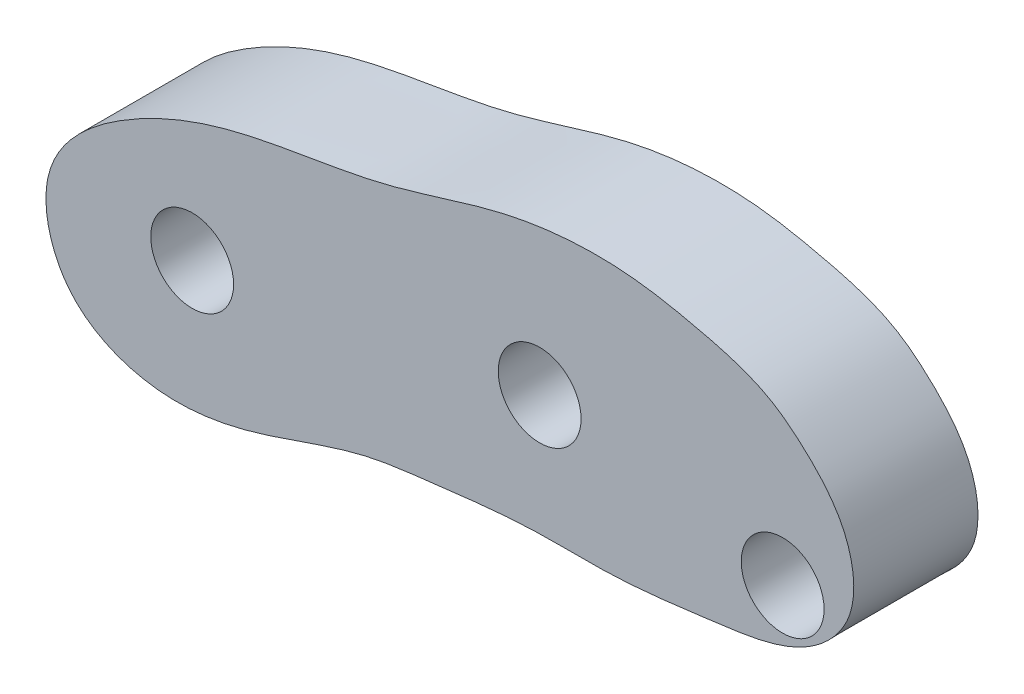
SolidWorks part; units mm, degrees
ref_plane "Спереди" through (0, 0, 0) normal (0, 0, 1) x (1, 0, 0)
ref_plane "Сверху" through (0, 0, 0) normal (0, 1, 0) x (1, 0, 0)
ref_plane "Справа" through (0, 0, 0) normal (1, 0, 0) x (0, 0, -1)
other "Configuration Table"
sketch "Sketch1" plane through (0, 0, 0) normal (0, 0, 1) x (1, 0, 0)
  circle A0 centre (-13.5931, 10.5462) radius 1
  circle A1 centre (-5.203, 11.9286) radius 1
  circle A2 centre (0.6645, 10.8833) radius 1
  spline S0 degree 3 poles (-16.811, 8.1991) (-17.5099, 10.9662) (-15.189, 12.8842) (-12.3116, 13.9653) (-9.1127, 14.2736) (-5.9881, 15.4672) (-3.3641, 15.6453) (-1.2088, 15.1992) (0.1933, 14.8289) (1.3653, 13.8719) (2.3167, 12.8084) (2.5268, 11.0508) (1.1519, 9.561) (-1.0265, 9.2978) (-3.2783, 8.9868) (-5.5579, 9.076) (-7.5114, 8.8227) (-9.8239, 8.5685) (-11.9834, 7.6073) (-14.5509, 7.2201) (-16.811, 8.1991) (-17.5099, 10.9662) (-15.189, 12.8842) knots -0.149336 -0.094857 -0.047917 0 0.064734 0.125809 0.207281 0.274075 0.347051 0.376812 0.42055 0.440494 0.476417 0.513364 0.545184 0.599503 0.653128 0.697206 0.749778 0.783749 0.850664 0.905143 0.952083 1 1.064734 1.125809 1.207281 only from (-17.0747, 10.5462) to (-17.0747, 10.5462)
  point P1 (0, 0)
  point P3 (0, 0)
  point P5 (0, 0)
  point P7 (-17.0747, 10.5462)
  point P8 (-8.4839, 8.7115)
  point P9 (-8.9402, 14.4708)
  point P12 (-18.3815, 2.6599)
  point P20 (-14.6624, 7.4619)
  point P24 (-16.5464, 8.4431)
  point P26 (0, 0)
  point P27 (-19.0584, 7.2853)
  point P28 (0, 0)
  point P30 (0, 0)
  point P32 (-16.2092, 11.9461)
  point P33 (-6.0322, 15.2952)
  point P34 (-12.5582, 13.761)
  point P35 (-2.7348, 15.4784)
  point P36 (-15.1228, 12.7306)
  dimension "D1" = 5.9599
  dimension "D2" = 14.2576
  dimension "D3" = 8.5032
extrude "Boss-Extrude1" add sketch "Sketch1" along normal blind 3 contours S0 | A0 | A1 | A2
ref_plane "Plane1" through (0, 0, 3) normal (0, 0, 1) x (1, 0, 0)
equation "\"R small\"= 2"
equation "\"R big\"= 4"
equation "\"width\"= 0.6"
equation "\"border width\"= 1"
equation "\"depth\"= 3"
